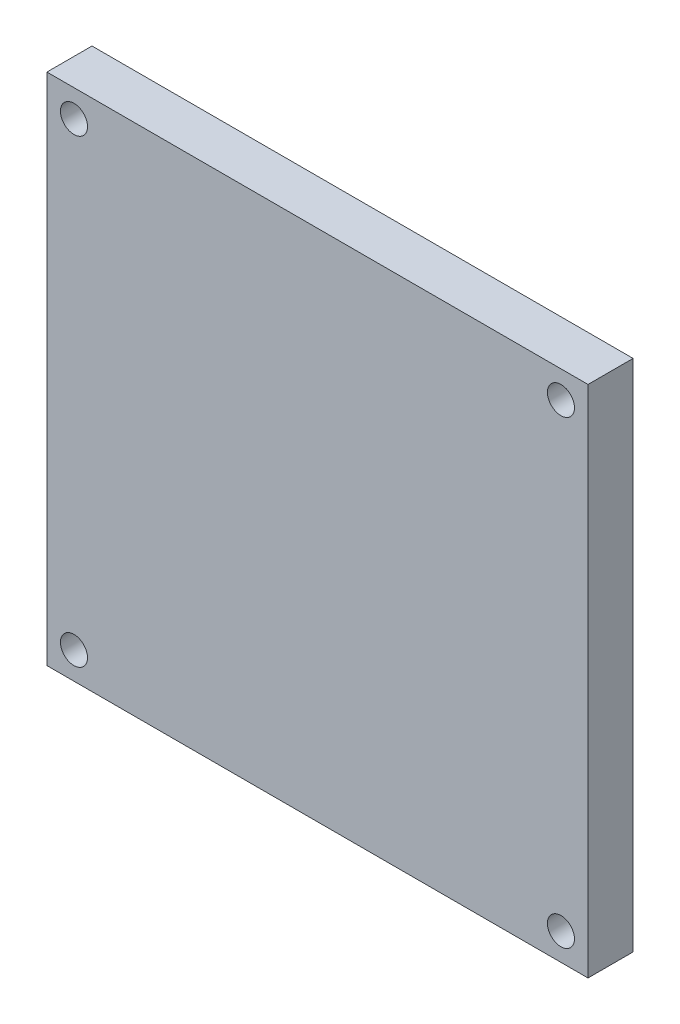
SolidWorks part; units mm, degrees
ref_plane "Front Plane" through (0, 0, 0) normal (0, 0, 1) x (1, 0, 0)
ref_plane "Top Plane" through (0, 0, 0) normal (0, 1, 0) x (1, 0, 0)
ref_plane "Right Plane" through (0, 0, 0) normal (1, 0, 0) x (0, 0, -1)
sketch "Sketch1" plane through (0, 0, 0) normal (0, 0, 1) x (1, 0, 0)
  line L1 (-30, -28.5) -> (30, -28.5)
  line L2 (-30, -28.5) -> (-30, 28.5)
  line L3 (-30, 28.5) -> (30, 28.5)
  line L4 (30, -28.5) -> (30, 28.5)
  line L5 (-30, -28.5) -> (30, 28.5) construction
  line L6 (-30, 28.5) -> (30, -28.5) construction
  point P0 (0, 0)
extrude "Boss-Extrude1" add sketch "Sketch1" along normal blind 5
sketch "Sketch2" plane through (0, 0, 0) normal (0, 0, -1) x (-1, 0, 0)
  text T0 "SLIDERX" font "Night Machine" height 8
extrude "Boss-Extrude2" add sketch "Sketch2" along normal blind 1
sketch "Sketch4" plane through (0, 0, 0) normal (0, 0, -1) x (-1, 0, 0)
  circle A0 centre (-27, 25.5) radius 2.51
  circle A1 centre (27, 25.5) radius 2.51
  circle A2 centre (27, -25.5) radius 2.51
  circle A3 centre (-27, -25.5) radius 2.51
extrude "Cut-Extrude1" cut sketch "Sketch4" against normal blind 1.5
sketch "Sketch5" plane through (0, 0, 0) normal (0, 0, -1) x (-1, 0, 0)
  circle A0 centre (-27, 25.5) radius 1.5
  circle A1 centre (27, 25.5) radius 1.5
  circle A2 centre (27, -25.5) radius 1.5
  circle A3 centre (-27, -25.5) radius 1.5
extrude "Cut-Extrude2" cut sketch "Sketch5" against normal up to surface (5 mm away) up to face at (0, 0, 5)
